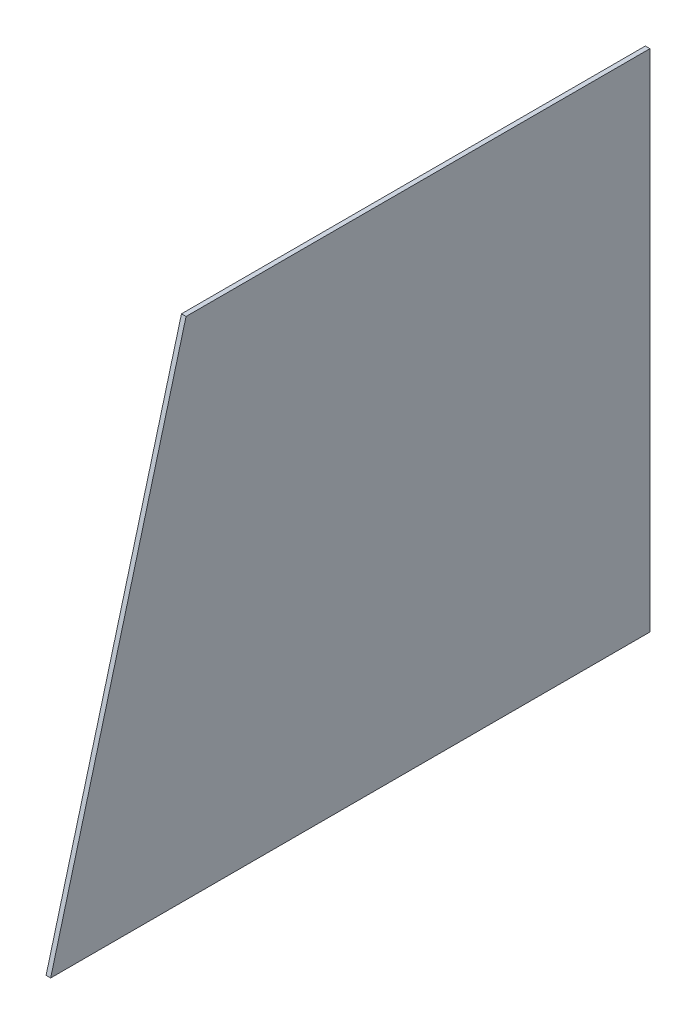
SolidWorks part; units mm, degrees
ref_plane "Front Plane" through (0, 0, 0) normal (0, 0, 1) x (1, 0, 0)
ref_plane "Top Plane" through (0, 0, 0) normal (0, 1, 0) x (1, 0, 0)
ref_plane "Right Plane" through (0, 0, 0) normal (1, 0, 0) x (0, 0, -1)
sketch "Sketch1" plane through (0, 0, 0) normal (1, 0, 0) x (0, 0, -1)
  line L0 (-196.0981, -165.3272) -> (-107.4995, 165.3272)
  line L1 (193.0981, -165.3272) -> (-196.0981, -165.3272)
  line L2 (-107.4995, 165.3272) -> (193.0981, 165.3272)
  line L3 (193.0981, 165.3272) -> (196.0981, 165.3272)
  line L4 (196.0981, 165.3272) -> (196.0981, -165.3272)
  line L5 (196.0981, -165.3272) -> (193.0981, -165.3272)
extrude "Boss-Extrude1" add sketch "Sketch1" along normal blind 3
